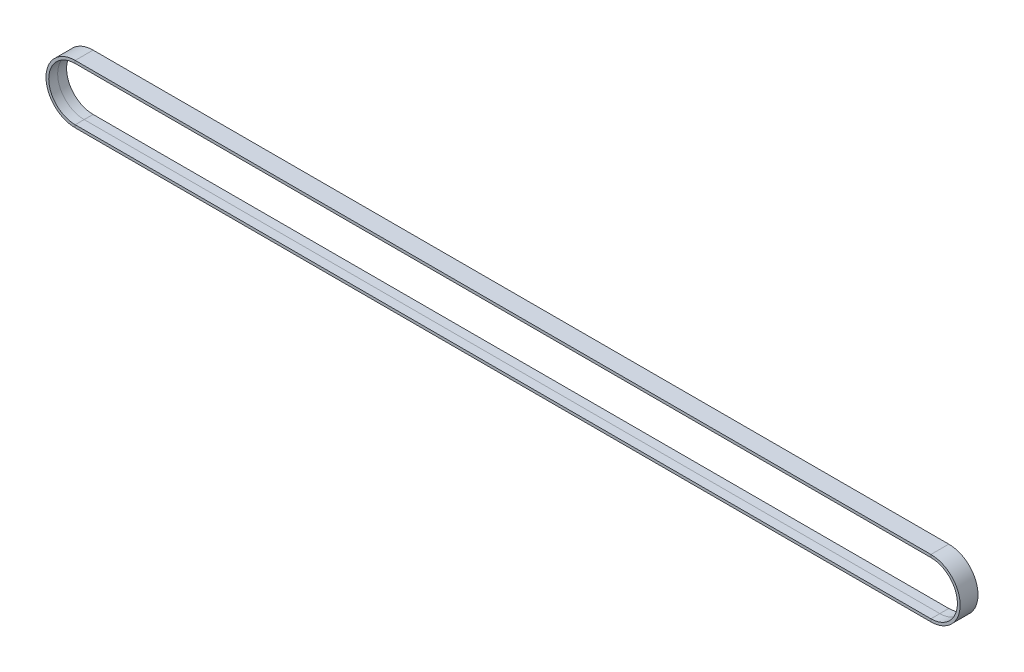
SolidWorks part; units mm, degrees
ref_plane "正面" through (0, 0, 0) normal (0, 0, 1) x (1, 0, 0)
ref_plane "平面" through (0, 0, 0) normal (0, 1, 0) x (1, 0, 0)
ref_plane "右側面" through (0, 0, 0) normal (1, 0, 0) x (0, 0, -1)
sketch "ｽｹｯﾁ2" plane through (0, 0, 0) normal (0, 0, 1) x (1, 0, 0)
  line L0 (0, 0) -> (1, 0) construction
  line L1 (0, 0) -> (0, 1) construction
  line L2 (0, -13.345) -> (-431, -13.345)
  line L3 (-431, 13.345) -> (0, 13.345)
  arc A0 (0, 13.345) -> (0, -13.345) centre (0, 0) cw
  arc A1 (-431, -13.345) -> (-431, 13.345) centre (-431, 0) cw
sketch3d "3Dｽｹｯﾁ3"
  line L0 (-431, 13.345, 0) -> (0, 13.345, 0) construction
  line L1 (0, 13.345, 0) -> (0, 13.345, -4.5)
  line L2 (0, 13.345, -4.5) -> (0, 14.715, -4.5)
  line L3 (0, 14.715, -4.5) -> (0, 14.715, 4.5)
  line L4 (0, 14.715, 4.5) -> (0, 13.345, 4.5)
  line L5 (0, 13.345, 4.5) -> (0, 13.345, 0)
  dimension "D1" = 1.37
  dimension "D2" = 9
  dimension "D3" = 4.5
sweep "ｽｲｰﾌﾟ1" add profiles "3Dｽｹｯﾁ3" path "ｽｹｯﾁ2"
